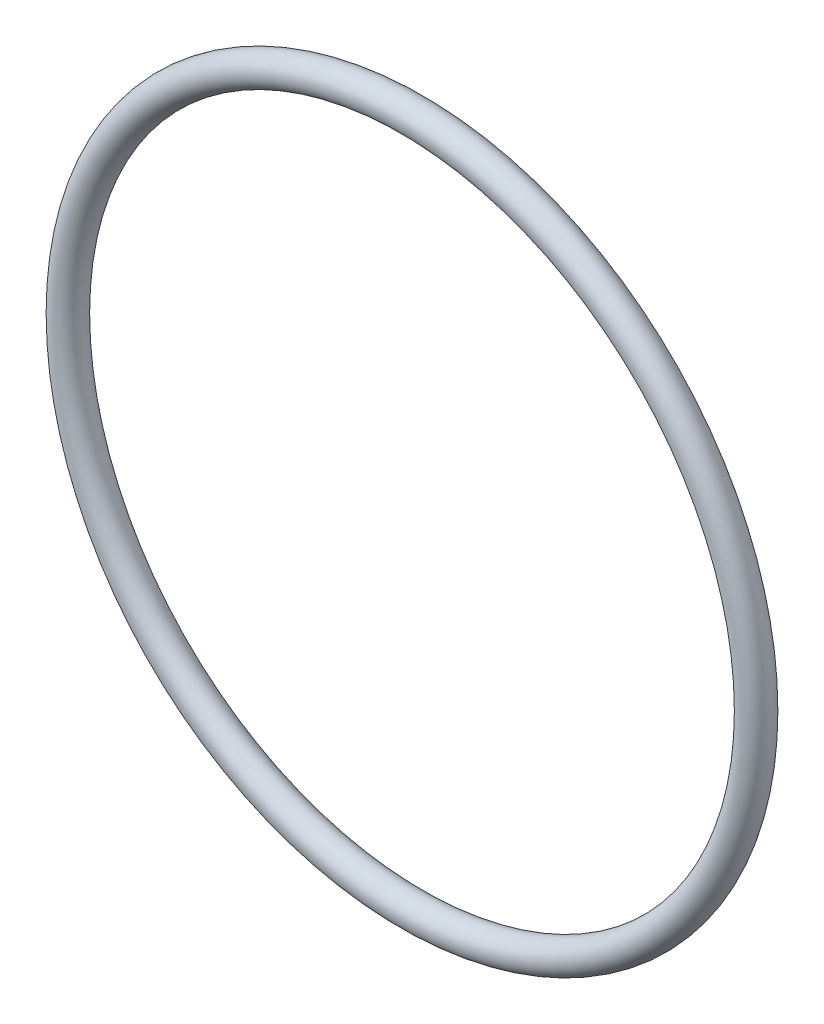
SolidWorks part; units mm, degrees
material "Rubber"
ref_plane "Front Plane" through (0, 0, 0) normal (0, 0, 1) x (1, 0, 0)
ref_plane "Top Plane" through (0, 0, 0) normal (0, 1, 0) x (1, 0, 0)
ref_plane "Right Plane" through (0, 0, 0) normal (1, 0, 0) x (0, 0, -1)
sketch "Sketch5" plane through (0, 0, 0) normal (0, 0, 1) x (1, 0, 0)
  circle A0 centre (0, 0) radius 36.4681
  dimension "D1" = 72.9361
sketch "Sketch6" plane through (0, 0, 0) normal (0, 1, 0) x (1, 0, 0)
  line L0 (-36.4681, 0) -> (36.4681, 0) construction
  circle A0 centre (36.4681, 0) radius 1.6319
  point P4 (0, 0)
  point P5 (50.7335, 0)
  point P6 (0, 0)
  dimension "D1" = 3.2639
sweep "Sweep1" add profiles "Sketch6" path "Sketch5"
